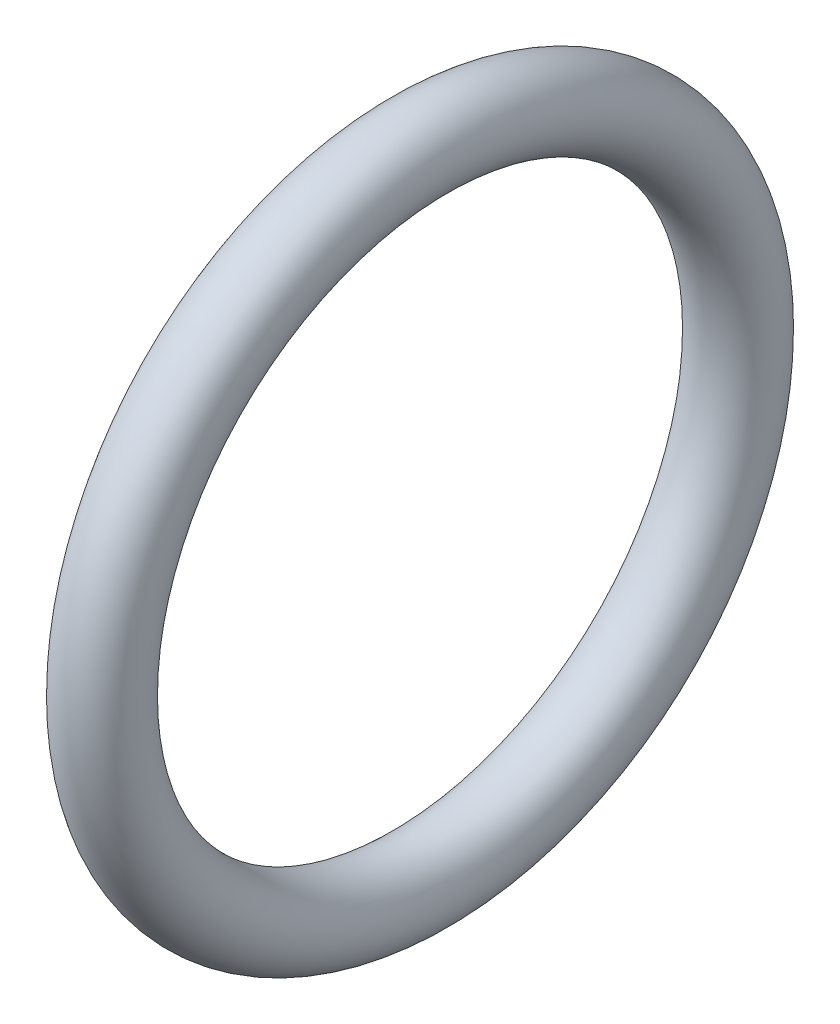
SolidWorks part; units mm, degrees
ref_plane "Face" through (0, 0, 0) normal (0, 0, 1) x (1, 0, 0)
ref_plane "Dessus" through (0, 0, 0) normal (0, 1, 0) x (1, 0, 0)
ref_plane "Droite" through (0, 0, 0) normal (1, 0, 0) x (0, 0, -1)
sketch "Esquisse1" plane through (0, 0, 0) normal (0, 0, 1) x (1, 0, 0)
  line L0 (-44.9344, 0) -> (38.3095, 0) construction
  circle A0 centre (-0.8641, 8.1) radius 1
  dimension "D2" = 2
  dimension "D1" = 8.1
revolve "Révolution1" add sketch "Esquisse1" angle 360 about L0
